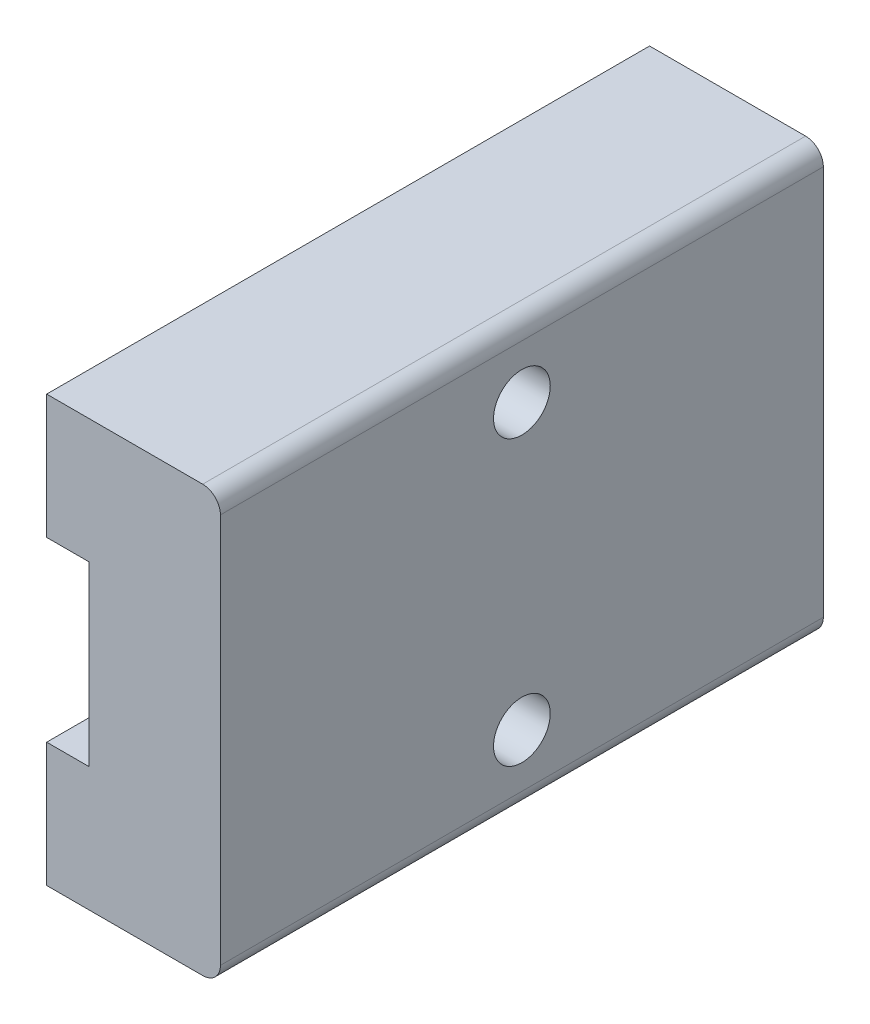
SolidWorks part; units mm, degrees
ref_plane "前视基准面" through (0, 0, 0) normal (0, 0, 1) x (1, 0, 0)
ref_plane "上视基准面" through (0, 0, 0) normal (0, 1, 0) x (1, 0, 0)
ref_plane "右视基准面" through (0, 0, 0) normal (1, 0, 0) x (0, 0, -1)
sketch "草图1" plane through (0, 0, 0) normal (0, 0, 1) x (1, 0, 0)
  line L1 (2.45, -6) -> (-2.45, -6)
  line L2 (2.45, -6) -> (2.45, 6)
  line L3 (2.45, 6) -> (-2.45, 6)
  line L4 (-2.45, -6) -> (-2.45, 6)
  line L5 (2.45, -6) -> (-2.45, 6) construction
  line L6 (2.45, 6) -> (-2.45, -6) construction
  point P0 (0, 0)
  dimension "D1" = 12
  dimension "D2" = 4.9
extrude "凸台-拉伸1" add sketch "草图1" along normal blind 17
sketch "草图2" plane through (0, 0, 17) normal (0, 0, 1) x (1, 0, 0)
  line L0 (-2.45, -2.5) -> (-1.25, -2.5)
  line L1 (-2.45, 6) -> (-2.45, -6) construction
  line L2 (-1.25, -2.5) -> (-1.25, 2.5)
  line L3 (-1.25, 2.5) -> (-2.45, 2.5)
  line L4 (-2.45, 2.5) -> (-2.45, -2.5)
  dimension "D1" = 5
  dimension "D2" = 1.2
  dimension "D3" = 2.5
extrude "切除-拉伸1" cut sketch "草图2" against normal through all
fillet "圆角1" radius 0.5 2 edges at (2.45, 6, 8.5) (2.45, -6, 8.5)
hole_wizard "M2 螺纹孔1" positions "草图5" profile "草图6" tap size "M2" standard "GB"
sketch "草图5" plane through (2.45, 0, 0) normal (1, 0, 0) x (0, 0, -1)
  line L0 (-8.5, 5.5) -> (-8.5, -5.5) construction
  line L1 (0, 5.5) -> (-17, 5.5) construction
  line L2 (-17, -5.5) -> (0, -5.5) construction
  point P0 (-8.5, 4)
  point P2 (-8.5, -4)
  point P13 (0, 0)
  point P14 (0, 0)
  dimension "D1" = 8
  dimension "D2" = 4
sketch "草图6" plane through (2.45, 4, 8.5) normal (0, 1, 0) x (0, 0, -1)
  line L0 (0, 0) -> (0, 2.6807)
  line L1 (0, 2.6807) -> (0.8, 2.2)
  line L2 (0.8, 2.2) -> (0.8, 0)
  line L5 (0.8, 0) -> (0, 0)
  line L10 (0, 2.6807) -> (-0.8, 2.2) construction
  line L11 (0, -6.35) -> (0, 107.95) construction
  dimension "螺纹孔钻头直径" = 1.6
  dimension "螺纹孔钻头深度" = 2.2
  dimension "导头角度" = 118
cosmetic thread "孔螺蚊线1" parameters "D1"=2, "D2"=2
cosmetic thread "孔螺蚊线2" parameters "D1"=2, "D2"=2
